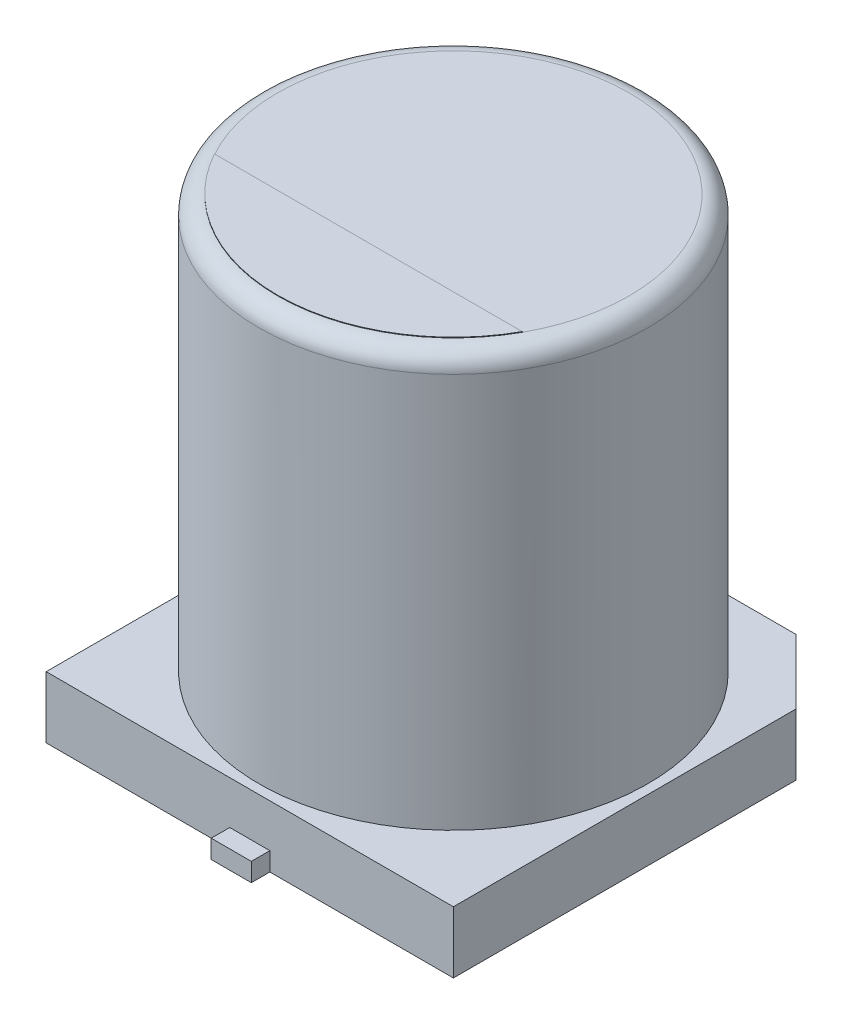
SolidWorks part; units mm, degrees
ref_plane "Front Plane" through (0, 0, 0) normal (0, 0, 1) x (1, 0, 0)
ref_plane "Top Plane" through (0, 0, 0) normal (0, 1, 0) x (1, 0, 0)
ref_plane "Right Plane" through (0, 0, 0) normal (1, 0, 0) x (0, 0, -1)
sketch "Sketch2" plane through (0, 0, 0) normal (0, 1, 0) x (1, 0, 0)
  line L0 (0, 0) -> (0, 2.085) construction
  line L1 (0, 0) -> (2.9643, 0) construction
  line L2 (3.3, -3.3) -> (-3.3, -3.3)
  line L3 (-3.3, -3.3) -> (-3.3, 2.25)
  line L4 (-3.3, 2.25) -> (-2.25, 3.3)
  line L5 (-2.25, 3.3) -> (2.25, 3.3)
  line L6 (2.25, 3.3) -> (3.3, 2.25)
  line L7 (3.3, 2.25) -> (3.3, -3.3)
  line L8 (0, -3.3) -> (0, -0.9795) construction
  line L9 (0, 3.3) -> (0, 2.1922) construction
  line L10 (-0.2934, -3.3) -> (-0.2934, 3.3) construction
  line L11 (-0.2934, 0) -> (-0.8682, 0) construction
  dimension "D1" = 6.6
  dimension "D2" = 6.6
  dimension "D3" = 4.5
extrude "Boss-Extrude1" add sketch "Sketch2" along normal blind 1
sketch "Sketch3" plane through (0, 0, 0) normal (0, 1, 0) x (1, 0, 0)
  circle A0 centre (0, 0) radius 3.15
  dimension "D1" = 6.3
extrude "Boss-Extrude2" add sketch "Sketch3" along normal blind 7.7 contours A0
fillet "Fillet1" radius 0.3 1 edges at (0, 7.7, 3.15)
sketch "Sketch4" plane through (0, 0, 0) normal (0, 1, 0) x (1, 0, 0)
  line L0 (0, 0) -> (5.065, 0) construction
  line L1 (0.325, 3.6) -> (-0.325, 3.6)
  line L2 (0.325, -0.8) -> (-0.325, -0.8)
  line L3 (0.325, -0.8) -> (0.325, -3.6)
  line L4 (0.325, -3.6) -> (-0.325, -3.6)
  line L5 (-0.325, -0.8) -> (-0.325, -3.6)
  line L6 (0.325, -0.8) -> (-0.325, -3.6) construction
  line L7 (0.325, -3.6) -> (-0.325, -0.8) construction
  line L8 (-0.325, 0.8) -> (-0.325, 3.6)
  line L9 (0.325, 0.8) -> (-0.325, 0.8)
  line L10 (0.325, 0.8) -> (0.325, 3.6)
  line L11 (0.325, 3.6) -> (-0.325, 0.8) construction
  line L12 (0.325, 0.8) -> (-0.325, 3.6) construction
  point P1 (0, -2.2)
  point P12 (0, 2.2)
  dimension "D1" = 0.65
  dimension "D2" = 2.8
  dimension "D3" = 1.6
extrude "Boss-Extrude3" add sketch "Sketch4" along normal blind 0.3
ref_plane "Plane1" through (0, 7.7, 0) normal (0, 1, 0) x (1, 0, 0)
sketch "Sketch5" plane through (0, 7.7, 0) normal (0, 1, 0) x (1, 0, 0)
  line L0 (-2.4946, -1.3782) -> (2.4946, -1.3782)
  circle A0 centre (0, 0) radius 2.85 construction
  arc A1 (-2.4946, -1.3782) -> (2.4946, -1.3782) centre (0, 0) ccw
extrude "Boss-Extrude4" add sketch "Sketch5" along normal blind 0.01
